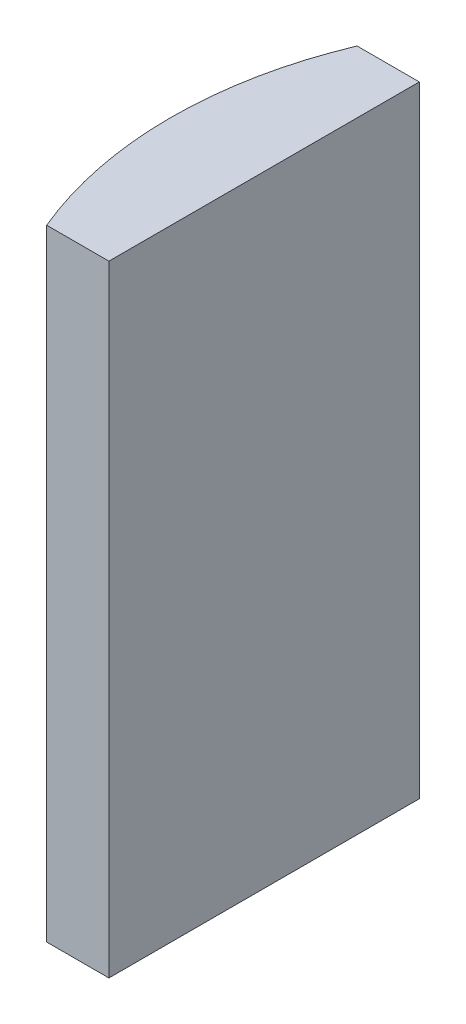
SolidWorks part; units mm, degrees
ref_plane "前视基准面" through (0, 0, 0) normal (0, 0, 1) x (1, 0, 0)
ref_plane "上视基准面" through (0, 0, 0) normal (0, 1, 0) x (1, 0, 0)
ref_plane "右视基准面" through (0, 0, 0) normal (1, 0, 0) x (0, 0, -1)
sketch "草图1" plane through (0, 0, 0) normal (0, 1, 0) x (1, 0, 0)
  line L0 (10.7432, 0) -> (-19.1624, 0) construction
  line L1 (-7.5689, 5) -> (-5.5648, 5)
  line L2 (-7.5689, -5) -> (-5.5648, -5)
  line L3 (-5.5648, 5) -> (-5.5648, -5)
  arc A0 (-7.5689, 5) -> (-7.5689, -5) centre (4.3552, 0) ccw
  point P19 (-8.5748, 0)
  point P20 (-5.5648, 0)
  dimension "D2" = 5
  dimension "D3" = 12.93
  dimension "D4" = 3.01
  dimension "D1" = 5
extrude "凸台-拉伸1" add sketch "草图1" along normal blind 20
